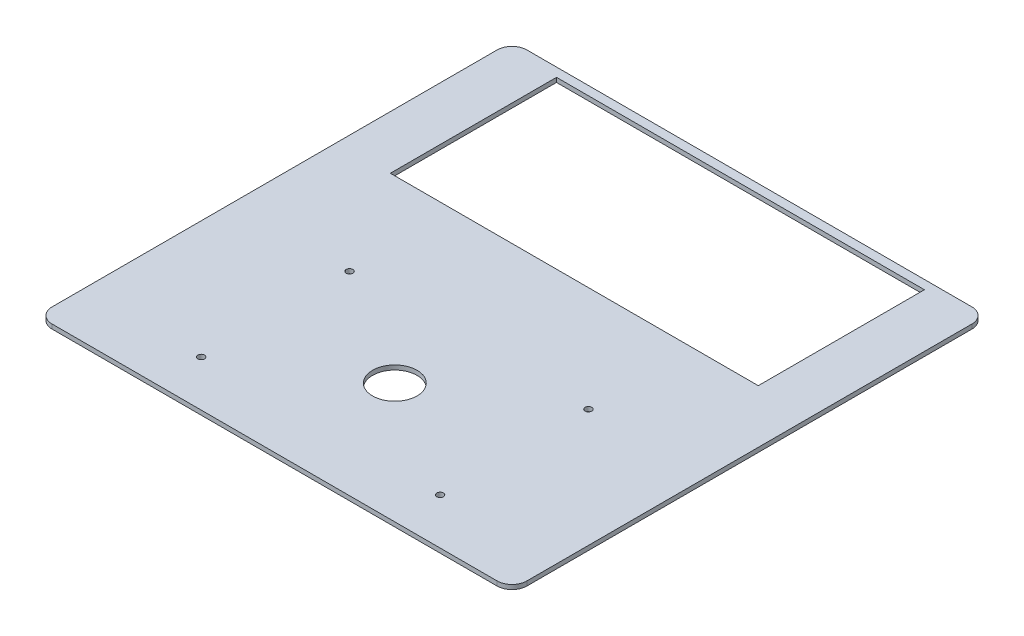
SolidWorks part; units mm, degrees
material "Cedar"
ref_plane "Front Plane" through (0, 0, 0) normal (0, 0, 1) x (1, 0, 0)
ref_plane "Top Plane" through (0, 0, 0) normal (0, 1, 0) x (1, 0, 0)
ref_plane "Right Plane" through (0, 0, 0) normal (1, 0, 0) x (0, 0, -1)
sketch "Sketch1" plane through (0, 0, 0) normal (0, 1, 0) x (1, 0, 0)
  line L0 (111.1, 83.14) -> (111.1, 84.07)
  line L1 (0, 0) -> (111.1, 0)
  line L2 (0, 0) -> (0, 83.14)
  line L3 (0, 83.14) -> (111.1, 83.14)
  line L4 (111.1, 0) -> (111.1, 83.14)
  line L5 (111.1, 0) -> (111.1, -0.93)
  line L6 (111.1, -0.93) -> (167.2, -0.93)
  line L7 (167.2, -0.93) -> (167.2, 84.07)
  line L8 (167.2, 84.07) -> (111.1, 84.07)
  line L9 (169.2, 97.57) -> (-78.8, 97.57)
  line L10 (169.2, -3.43) -> (-78.8, -3.43)
  line L11 (169.2, -14.43) -> (169.2, 97.57)
  line L12 (169.2, 86.57) -> (-78.8, 86.57)
  line L13 (-78.8, -14.43) -> (-78.8, 97.57)
  line L14 (169.2, -14.43) -> (-78.8, -14.43)
  line L16 (-114.8, 103.57) -> (205.2, 103.57)
  line L17 (-114.8, 103.57) -> (-114.8, -216.43)
  line L18 (-114.8, -216.43) -> (205.2, -216.43)
  line L19 (205.2, 103.57) -> (205.2, -216.43)
  line L20 (-54.8, -60.43) -> (145.2, -60.43)
  line L21 (-54.8, -60.43) -> (-54.8, -210.43)
  line L22 (-54.8, -210.43) -> (145.2, -210.43)
  line L23 (145.2, -60.43) -> (145.2, -210.43)
  circle A0 centre (101.6, 16) radius 1.65
  circle A1 centre (2.15, 2.15) radius 1.65
  circle A2 centre (33.15, 2.15) radius 1.65
  circle A3 centre (2.15, 53.15) radius 1.65
  circle A4 centre (57.1, 76.14) radius 1.65
  circle A5 centre (163.7, 2.57) radius 1.35
  circle A6 centre (114.7, 2.57) radius 1.35
  circle A7 centre (163.7, 60.57) radius 1.35
  circle A8 centre (114.7, 60.57) radius 1.35
  circle A9 centre (-14.3, -8.93) radius 1.65
  circle A10 centre (-66.8, -8.93) radius 1.65
  circle A11 centre (-14.3, 92.07) radius 1.65
  circle A12 centre (-66.8, 92.07) radius 1.65
  circle A13 centre (-35.3, -85.43) radius 2.25
  circle A14 centre (125.7, -85.43) radius 2.25
  circle A15 centre (125.7, -185.43) radius 2.25
  circle A16 centre (-35.3, -185.43) radius 2.25
  circle A17 centre (45.2, -135.43) radius 15
  dimension "D6" = 3.3
  dimension "D9" = 3.3
  dimension "D10" = 2
  dimension "D12" = 3.3
  dimension "D14" = 3.3
  dimension "D16" = 3.3
  dimension "D17" = 54
  dimension "D18" = 7
  dimension "D19" = 2.7
  dimension "D20" = 3.5
  dimension "D21" = 3.5
  dimension "D22" = 2.7
  dimension "D23" = 3.5
  dimension "D25" = 2.7
  dimension "D26" = 58
  dimension "D28" = 2.7
  dimension "D36" = 11
  dimension "D37" = 320
  dimension "D38" = 248
  dimension "D39" = 6
  dimension "D40" = 320
  dimension "D41" = 150
  dimension "D44" = 200
  dimension "D46" = 100
  dimension "D30" = 2
  dimension "D35" = 11
  dimension "D33" = 12
  dimension "D34" = 8
  dimension "D47" = 25
  dimension "D49" = 161
  dimension "D52" = 19.5
  dimension "D53" = 100
  dimension "D54" = 75
  dimension "D55" = 19.5
  dimension "D1" = 111.1
  dimension "D2" = 83.14
  dimension "D3" = 0.93
  dimension "D4" = 0.93
  dimension "D5" = 56.1
  dimension "D7" = 9.5
  dimension "D8" = 16
  dimension "D11" = 2.15
  dimension "D13" = 31
  dimension "D15" = 51
  dimension "D24" = 3.6
  dimension "D27" = 58
  dimension "D29" = 2
  dimension "D31" = 90
  dimension "D32" = 2.5
  dimension "D42" = 6
  dimension "D43" = 36
  dimension "D45" = 60
  dimension "D48" = 0
  dimension "D50" = 161
  dimension "D51" = 0
extrude "Boss-Extrude1" add sketch "Sketch1" along normal blind 3 contours L19 L16 L17 L18 L11 L14 L13 L9 L20 L23 L22 L21 | L23 L20 L21 L22 A17 A16 A15 A14 A13
fillet "Fillet1" radius 10 4 edges at (205.2, 1.5, -103.57) (-114.8, 1.5, -103.57) (205.2, 1.5, 216.43) (-114.8, 1.5, 216.43)
